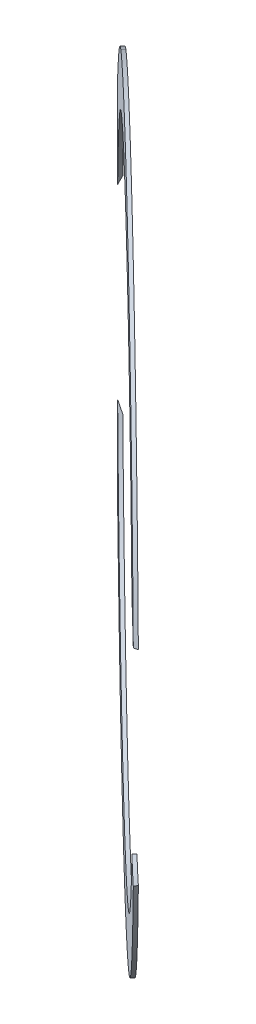
SolidWorks part; units mm, degrees
ref_plane "Front" through (0, 0, 0) normal (0, 0, 1) x (1, 0, 0)
ref_plane "Top" through (0, 0, 0) normal (0, 1, 0) x (1, 0, 0)
ref_plane "Right" through (0, 0, 0) normal (1, 0, 0) x (0, 0, -1)
sketch "Sketch2" plane through (-164.2276, 0, 170.5889) normal (-0.6935, 0, 0.7204) x (0.7204, 0, 0.6935)
  circle A0 centre (0, 0) radius 298.479
  circle A1 centre (0, 0) radius 257.204
  circle A2 centre (0, 0) radius 298.479 construction
  dimension "D1" = 41.275
  dimension "D2" = 596.958
extrude "Extrude1" add sketch "Sketch2" against normal blind 3.2258
sketch "Sketch3" plane through (0, 0, 0) normal (0, 0, 1) x (1, 0, 0)
  circle A0 centre (0, 0) radius 101.6
  dimension "D1" = 203.2
extrude "Cut-Extrude1" cut sketch "Sketch3" along normal through all
sketch "Sketch4" plane through (0, 0, 0) normal (0, 0, 1) x (1, 0, 0)
  circle A0 centre (0, 0) radius 381
  dimension "D1" = 762
extrude "Cut-Extrude2" cut sketch "Sketch4" along normal blind 2.032 and the other way through all
sketch "Sketch5" plane through (0, 0, 0) normal (0, 1, 0) x (1, 0, 0)
  line L0 (0, 0) -> (-381, 0) construction
  line L1 (-373.3022, -76.2) -> (-525.7022, -76.2)
  line L2 (0, 0) -> (0, -303.6018) construction
  line L3 (-525.7022, -76.2) -> (-525.7022, 76.2)
  line L4 (-525.7022, 76.2) -> (-373.3022, 76.2)
  arc A1 (50.8, -377.5981) -> (-379.2553, 36.4203) centre (0, 0) ccw construction
  circle A2 centre (0, 0) radius 381 construction
  ellipse E0 centre (-365.7003, 0) end of major axis (-365.7003, -92.9745) minor radius 13.2677 (-373.3022, 76.2) -> (-373.3022, -76.2) ccw
  dimension "D1" = 2.032
  dimension "D2" = 152.4
revolve "Cut-Revolve5" cut sketch "Sketch5" angle 360 about L2
sketch "Sketch6" plane through (-164.2276, 0, 170.5889) normal (-0.6935, 0, 0.7204) x (0.7204, 0, 0.6935)
  line L0 (-243.036, 168.7622) -> (-243.036, 265.6457)
  line L1 (-243.036, 265.6457) -> (-136.0959, 265.6457)
  line L2 (-243.036, 84.1867) -> (-243.036, 168.7622) construction
  line L3 (-243.036, -168.7622) -> (-243.036, -265.6457)
  line L4 (-243.036, -265.6457) -> (-136.0959, -265.6457)
  line L5 (-243.036, -168.7622) -> (-243.036, -84.1867) construction
  spline S0 degree 3 poles (460.0142, -1669.2549) (-329.4056, -496.0774) (-409.1558, -17.9489) (-212.6997, 206.5343) (-204.273, 215.1521) (-190.9188, 227.3794) (-186.3479, 231.3381) (-176.9571, 239.0116) (-172.1375, 242.7267) (-162.2259, 249.8902) (-157.1682, 253.3151) (-149.4118, 258.1737) (-146.7974, 259.7467) (-28.3139, 327.7117) (151.2046, 291.6111) (1224.8202, -1184.2241) knots -5.677693 -5.677693 -5.677693 -5.677693 0.25 0.25 0.5 0.5 0.625 0.625 0.75 0.75 0.875 0.875 0.9375 0.9375 3.671592 3.671592 3.671592 3.671592 only from (-243.036, 168.7622) to (-136.0959, 265.6457) construction
  spline S1 degree 3 poles (-243.036, 168.7622) (-236.0732, 178.8137) (-228.6001, 188.3655) (-212.6997, 206.5343) (-204.273, 215.1521) (-190.9188, 227.3794) (-186.3479, 231.3381) (-176.9571, 239.0116) (-172.1375, 242.7267) (-162.2259, 249.8902) (-157.1682, 253.3151) (-149.4118, 258.1737) (-146.7974, 259.7467) (-141.5015, 262.7845) (-138.8203, 264.2499) (-136.0959, 265.6457) knots 0 0 0 0 0.25 0.25 0.5 0.5 0.625 0.625 0.75 0.75 0.875 0.875 0.9375 0.9375 1 1 1 1
  spline S2 degree 3 poles (1190.3574, 1215.4894) (150.8757, -289.5664) (-27.5738, -328.1241) (-146.7794, -259.7573) (-149.3919, -258.1858) (-154.5614, -254.9483) (-157.1211, -253.2803) (-162.17, -249.8713) (-164.6607, -248.1295) (-172.0386, -242.8002) (-176.832, -239.1092) (-186.1885, -231.4728) (-190.7511, -227.5271) (-204.103, -215.3191) (-212.5581, -206.6882) (-222.558, -195.2715) (-224.5294, -192.9565) (-228.4139, -188.2624) (-230.3251, -185.8854) (-422.9286, 60.7425) (-256.973, 573.9199) (595.1286, 1604.4728) knots -2.692144 -2.692144 -2.692144 -2.692144 0.0625 0.0625 0.125 0.125 0.1875 0.1875 0.25 0.25 0.375 0.375 0.5 0.5 0.75 0.75 0.8125 0.8125 0.875 0.875 7.231549 7.231549 7.231549 7.231549 only from (-136.0959, -265.6457) to (-243.036, -168.7622) construction
  spline S3 degree 3 poles (-136.0959, -265.6457) (-138.8136, -264.2533) (-141.4901, -262.7908) (-146.7794, -259.7573) (-149.3919, -258.1858) (-154.5614, -254.9483) (-157.1211, -253.2803) (-162.17, -249.8713) (-164.6607, -248.1295) (-172.0386, -242.8002) (-176.832, -239.1092) (-186.1885, -231.4728) (-190.7511, -227.5271) (-204.103, -215.3191) (-212.5581, -206.6882) (-222.558, -195.2715) (-224.5294, -192.9565) (-228.4139, -188.2624) (-230.3251, -185.8854) (-235.951, -178.6814) (-239.5637, -173.7748) (-243.036, -168.7622) knots 0 0 0 0 0.0625 0.0625 0.125 0.125 0.1875 0.1875 0.25 0.25 0.375 0.375 0.5 0.5 0.75 0.75 0.8125 0.8125 0.875 0.875 1 1 1 1
extrude "Cut-Extrude3" cut sketch "Sketch6" against normal through all
split "Split1" bodies to split 115 116 resulting bodies 107 108
